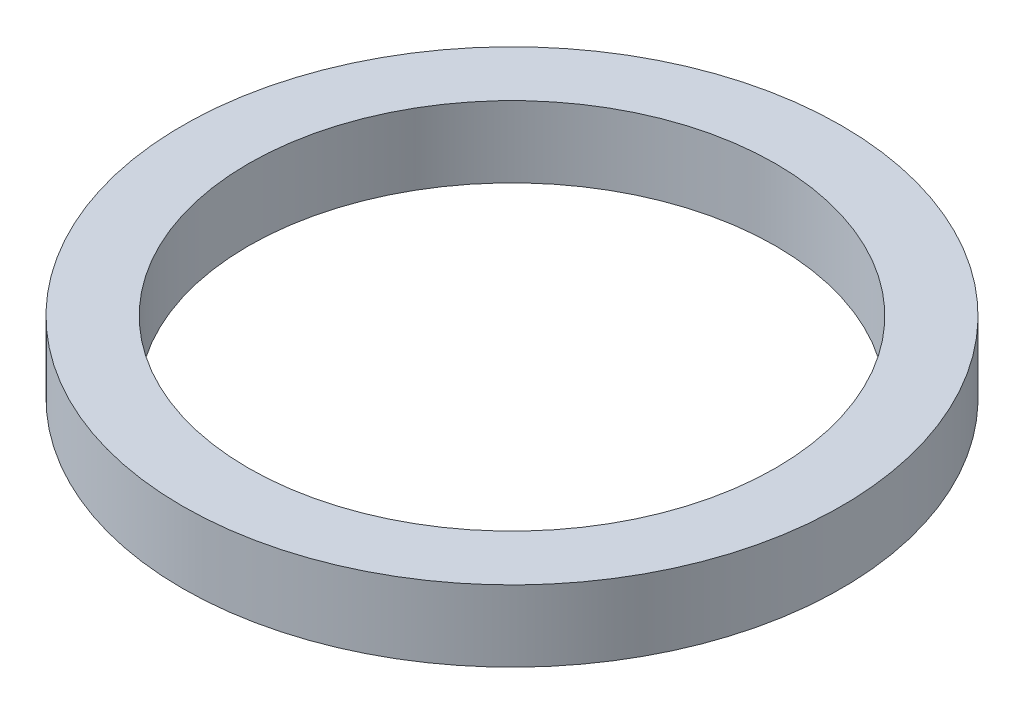
SolidWorks part; units mm, degrees
material "ABS"
ref_plane "Ebene vorne" through (0, 0, 0) normal (0, 0, 1) x (1, 0, 0)
ref_plane "Ebene oben" through (0, 0, 0) normal (0, 1, 0) x (1, 0, 0)
ref_plane "Ebene rechts" through (0, 0, 0) normal (1, 0, 0) x (0, 0, -1)
sketch "Skizze1" plane through (0, 0, 0) normal (0, 1, 0) x (1, 0, 0)
  circle A0 centre (0, 0) radius 9.25
  circle A1 centre (0, 0) radius 7.4
  dimension "D1" = 18.5
  dimension "D2" = 14.8
extrude "Aufsatz-Linear austragen1" add sketch "Skizze1" along normal blind 2
